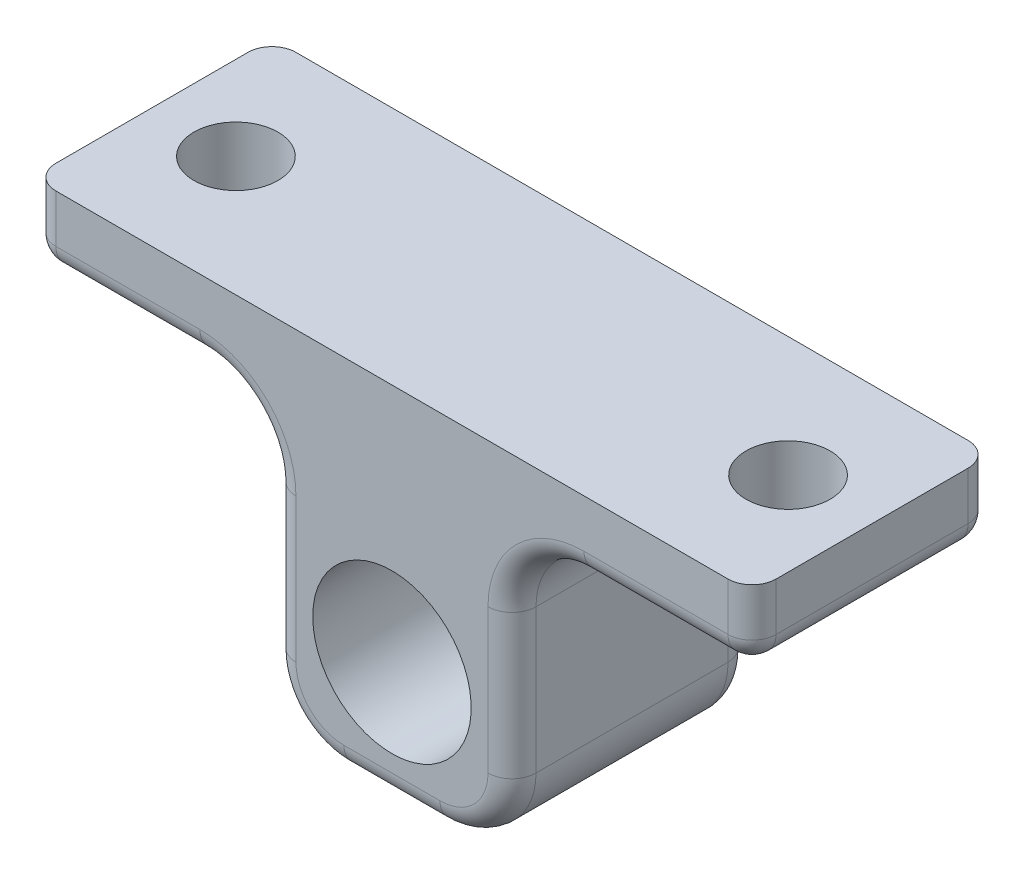
SolidWorks part; units mm, degrees
ref_plane "正面" through (0, 0, 0) normal (0, 0, 1) x (1, 0, 0)
ref_plane "平面" through (0, 0, 0) normal (0, 1, 0) x (1, 0, 0)
ref_plane "右側面" through (0, 0, 0) normal (1, 0, 0) x (0, 0, -1)
sketch "ｽｹｯﾁ1" plane through (0, 0, 0) normal (0, 0, 1) x (1, 0, 0)
  line L0 (0, 10) -> (0, -5)
  line L1 (5, -5) -> (-5, -5)
  line L2 (5, -5) -> (5, 10)
  line L3 (5, 10) -> (-5, 10)
  line L4 (-5, -5) -> (-5, 10)
  line L5 (5, 10) -> (15, 10)
  line L6 (5, 10) -> (5, 7)
  line L7 (5, 7) -> (15, 7)
  line L8 (15, 10) -> (15, 7)
  line L9 (-15, 10) -> (-15, 7)
  line L10 (-5, 7) -> (-15, 7)
  line L11 (-5, 10) -> (-5, 7)
  line L12 (-5, 10) -> (-15, 10)
  line L13 (5, -5) -> (5, 10)
  line L14 (-5, -5) -> (-5, 10)
  line L15 (5, 10) -> (15, 10)
  line L16 (15, 10) -> (5, 10)
  dimension "D1" = 15
  dimension "D2" = 10
  dimension "D5" = 3
  dimension "D6" = 10
extrude "ﾎﾞｽ - 押し出し1" add sketch "ｽｹｯﾁ1" along normal blind 10 contours L2 L3 L0 L1 | L8 L5 L2 L7 | L4 L1 L0 L3 | L4 L12 L9 L10
sketch "ｽｹｯﾁ2" plane through (0, 0, 0) normal (0, 0, -1) x (-1, 0, 0)
  circle A0 centre (0, 0) radius 3.3
  dimension "D1" = 6.6
extrude "ｶｯﾄ - 押し出し1" cut sketch "ｽｹｯﾁ2" against normal through all
sketch "ｽｹｯﾁ3" plane through (0, 7, 0) normal (0, -1, 0) x (1, 0, 0)
  line L0 (-15, 10) -> (-15, 0) construction
  line L1 (-5, 0) -> (-15, 0) construction
  line L2 (0, 0.3201) -> (0, 10.158)
  circle A0 centre (-11.5, 5) radius 1.75
  circle A1 centre (11.5, 5) radius 1.75
  dimension "D1" = 3.5
  dimension "D2" = 3.5
  dimension "D3" = 5
extrude "ｶｯﾄ - 押し出し2" cut sketch "ｽｹｯﾁ3" against normal through all contours A0 | A1
fillet "ﾌｨﾚｯﾄ1" radius 3 4 edges at (-5, 7, 5) (5, 7, 5) (-5, -5, 5) (5, -5, 5)
fillet "ﾌｨﾚｯﾄ2" radius 1 24 edges at (11.5, 7, 10) (11.5, 7, 0) (5.8787, 6.1213, 10) (5.8787, 6.1213, 0) (5, 1, 0) (5, 1, 10) (4.1213, -4.1213, 10) (4.1213, -4.1213, 0) (0, -5, 10) (0, -5, 0) (-4.1213, -4.1213, 10) (-4.1213, -4.1213, 0) (-5, 1, 10) (-5, 1, 0) (-5.8787, 6.1213, 10) (-5.8787, 6.1213, 0) (-15, 8.5, 0) (-15, 8.5, 10) (15, 8.5, 0) (15, 8.5, 10) (15, 7, 5) (-11.5, 7, 0) (-11.5, 7, 10) (-15, 7, 5)
